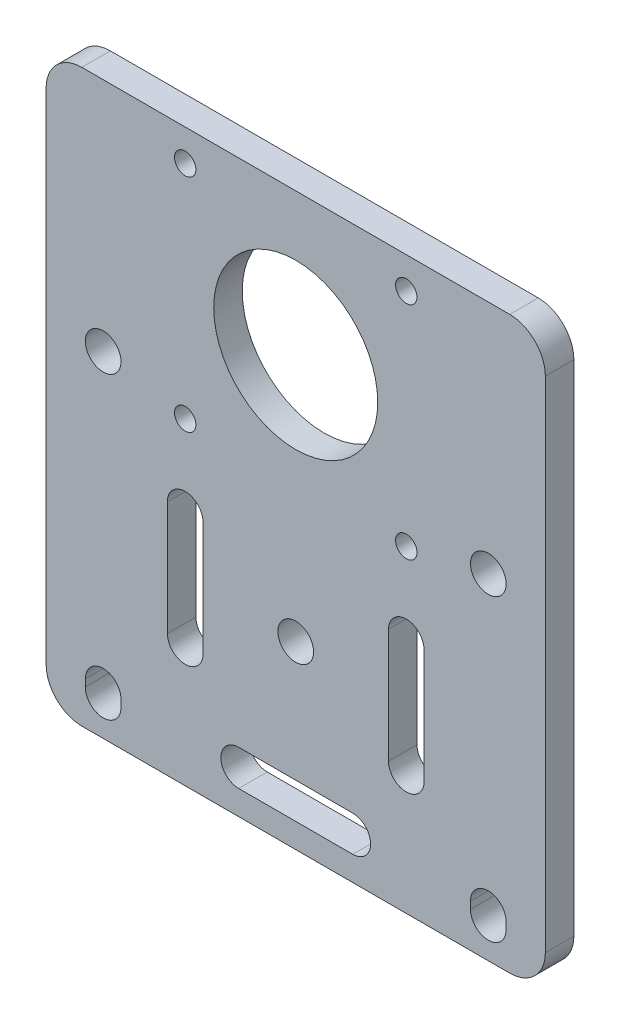
SolidWorks part; units mm, degrees
ref_plane "Front" through (0, 0, 0) normal (0, 0, 1) x (1, 0, 0)
ref_plane "Top" through (0, 0, 0) normal (0, 1, 0) x (1, 0, 0)
ref_plane "Right" through (0, 0, 0) normal (1, 0, 0) x (0, 0, -1)
sketch "Sketch4" plane through (0, 0, 0) normal (0, 0, 1) x (1, 0, 0)
  line L0 (-27, -34) -> (-27, -35) construction
  line L1 (-35, 40) -> (35, 40)
  line L2 (-35, 40) -> (-35, -40)
  line L3 (-35, -40) -> (35, -40)
  line L4 (35, 40) -> (35, -40)
  line L5 (-35, 40) -> (35, -40) construction
  line L6 (-35, -40) -> (35, 40) construction
  line L7 (-24.5, -34) -> (-24.5, -35)
  line L8 (-29.5, -34) -> (-29.5, -35)
  line L9 (0, -47.1607) -> (0, 39.6245) construction
  line L10 (27, -34) -> (27, -35) construction
  line L11 (24.5, -34) -> (24.5, -35)
  line L12 (29.5, -34) -> (29.5, -35)
  circle A0 centre (-27, 7) radius 2.5
  arc A1 (-24.5, -34) -> (-29.5, -34) centre (-27, -34) ccw
  arc A2 (-29.5, -35) -> (-24.5, -35) centre (-27, -35) ccw
  arc A3 (24.5, -34) -> (29.5, -34) centre (27, -34) cw
  arc A4 (29.5, -35) -> (24.5, -35) centre (27, -35) cw
  circle A5 centre (27, 7) radius 2.5
  point P0 (0, 0)
  point P10 (-27, -34.5)
  point P19 (27, -34.5)
  dimension "D3" = 27
  dimension "D6" = 2.5
  dimension "D1" = 70
  dimension "D2" = 80
  dimension "D4" = 41
  dimension "D5" = 1
  dimension "D7" = 5
extrude "Boss-Extrude2" add sketch "Sketch4" along normal blind 4
sketch "Sketch5" plane through (0, 0, 4) normal (0, 0, 1) x (1, 0, 0)
  line L0 (0, 46.583) -> (0, -17.262) construction
  line L1 (-44.8343, 20.0767) -> (52.8956, 20.0767) construction
  line L2 (-26.4123, 4.5701) -> (26.4123, -34.0701) construction
  line L3 (-27, -34.5) -> (27, 5) construction
  line L4 (-8, -34.0701) -> (8, -34.0701) construction
  line L5 (-8, -31.5701) -> (8, -31.5701)
  line L6 (-8, -36.5701) -> (8, -36.5701)
  line L7 (-15.5, -6.75) -> (-15.5, -22.75) construction
  line L8 (-13, -6.75) -> (-13, -22.75)
  line L9 (-18, -6.75) -> (-18, -22.75)
  line L10 (0, -5.3618) -> (0, -23.281) construction
  line L11 (15.5, -6.75) -> (15.5, -22.75) construction
  line L12 (13, -6.75) -> (13, -22.75)
  line L13 (18, -6.75) -> (18, -22.75)
  circle A0 centre (0, 20.0767) radius 11.5
  circle A1 centre (27, 7) radius 2.5 construction
  circle A2 centre (-15.5, 35.5767) radius 1.5
  circle A9 centre (15.5, 35.5767) radius 1.5
  circle A10 centre (15.5, 4.5767) radius 1.5
  circle A11 centre (-15.5, 4.5767) radius 1.5
  circle A12 centre (0, -14.75) radius 2.5
  arc A13 (-8, -31.5701) -> (-8, -36.5701) centre (-8, -34.0701) ccw
  arc A14 (8, -36.5701) -> (8, -31.5701) centre (8, -34.0701) ccw
  arc A15 (-13, -6.75) -> (-18, -6.75) centre (-15.5, -6.75) ccw
  arc A16 (-18, -22.75) -> (-13, -22.75) centre (-15.5, -22.75) ccw
  arc A17 (13, -6.75) -> (18, -6.75) centre (15.5, -6.75) cw
  arc A18 (18, -22.75) -> (13, -22.75) centre (15.5, -22.75) cw
  point P26 (0, -34.0701)
  point P33 (-15.5, -14.75)
  point P42 (15.5, -14.75)
  dimension "D1" = 23
  dimension "D3" = 3
  dimension "D6" = 16
  dimension "D7" = 2.5
  dimension "D9" = 2.5
  dimension "D10" = 5
  dimension "D2" = 30
  dimension "D4" = 15.5
  dimension "D5" = 15.5
  dimension "D8" = 16
extrude "Cut-Extrude2" cut sketch "Sketch5" against normal through all
fillet "Fillet1" radius 5 4 edges at (-35, -40, 2) (35, -40, 2) (35, 40, 2) (-35, 40, 2)
